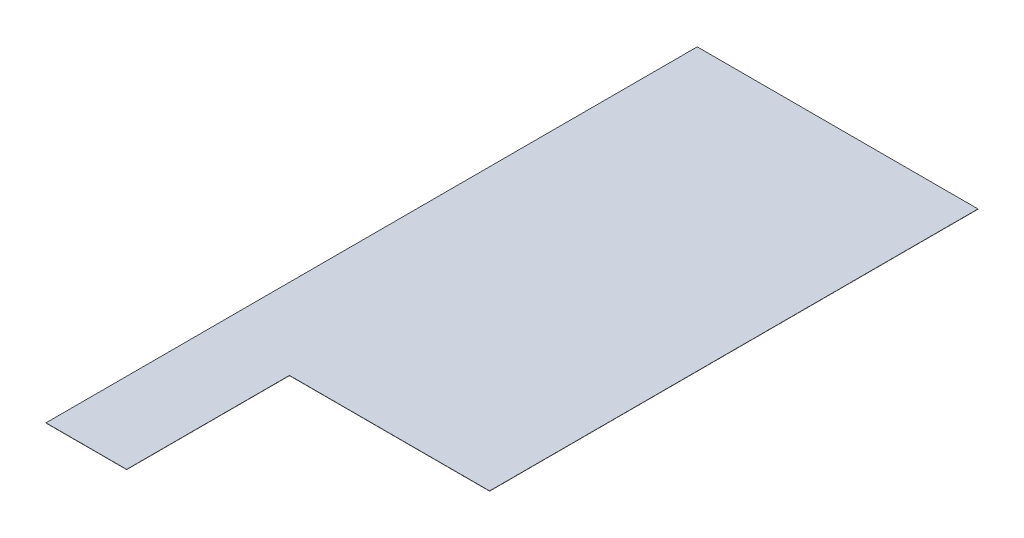
SolidWorks part; units mm, degrees
material "PE High Density Film"
ref_plane "Front Plane" through (0, 0, 0) normal (0, 0, 1) x (1, 0, 0)
ref_plane "Top Plane" through (0, 0, 0) normal (0, 1, 0) x (1, 0, 0)
ref_plane "Right Plane" through (0, 0, 0) normal (1, 0, 0) x (0, 0, -1)
sketch "Sketch1" plane through (0, 0, 0) normal (0, 1, 0) x (1, 0, 0)
  line L1 (-1051.306, -2438.4) -> (1051.306, -2438.4)
  line L2 (-1051.306, -2438.4) -> (-1051.306, 2438.4)
  line L3 (-1051.306, 2438.4) -> (1051.306, 2438.4)
  line L4 (1051.306, -2438.4) -> (1051.306, 2438.4)
  line L5 (-1051.306, -2438.4) -> (1051.306, 2438.4) construction
  line L6 (-1051.306, 2438.4) -> (1051.306, -2438.4) construction
  point P0 (0, 0)
  dimension "D1" = 4876.8
  dimension "D2" = 2102.612
extrude "Boss-Extrude1" add sketch "Sketch1" along normal blind 1.5875
sketch "Sketch2" plane through (0, 1.5875, 0) normal (0, 1, 0) x (1, 0, 0)
  line L1 (1051.306, -2438.4) -> (-447.294, -2438.4)
  line L2 (1051.306, -2438.4) -> (1051.306, -1219.2)
  line L3 (1051.306, -1219.2) -> (-447.294, -1219.2)
  line L4 (-447.294, -2438.4) -> (-447.294, -1219.2)
  dimension "D1" = 1498.6
  dimension "D2" = 1219.2
extrude "Cut-Extrude1" cut sketch "Sketch2" against normal through all both and the other way through all
